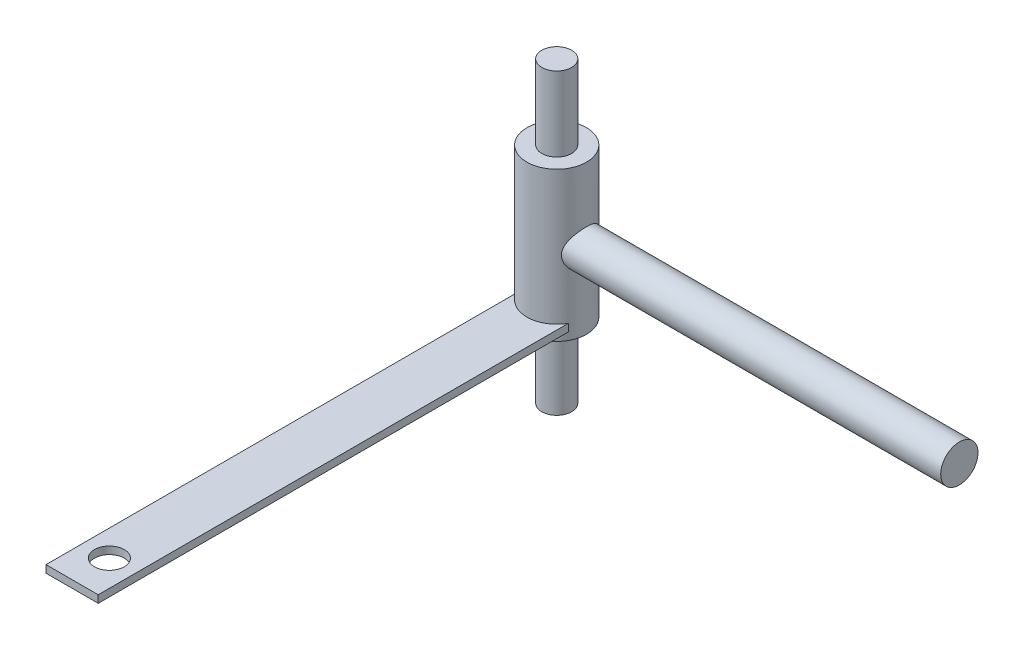
SolidWorks part; units mm, degrees
ref_plane "Front Plane" through (0, 0, 0) normal (0, 0, 1) x (1, 0, 0)
ref_plane "Top Plane" through (0, 0, 0) normal (0, 1, 0) x (1, 0, 0)
ref_plane "Right Plane" through (0, 0, 0) normal (1, 0, 0) x (0, 0, -1)
sketch "Sketch1" plane through (0, 0, 0) normal (0, 1, 0) x (1, 0, 0)
  circle A0 centre (0, 0) radius 4
  dimension "D1" = 8
extrude "Boss-Extrude1" add sketch "Sketch1" along normal mid plane 80
sketch "Sketch3" plane through (0, 0, 0) normal (0, 1, 0) x (1, 0, 0)
  circle A0 centre (0, 0) radius 8
  dimension "D1" = 16
extrude "Boss-Extrude2" add sketch "Sketch3" along normal mid plane 40
sketch "Sketch4" plane through (0, 0, 0) normal (1, 0, 0) x (0, 0, -1)
  circle A0 centre (0, 0) radius 5
  dimension "D1" = 10
extrude "Boss-Extrude3" add sketch "Sketch4" along normal blind 108
sketch "Sketch5" plane through (0, 0, 0) normal (0, 0, 1) x (1, 0, 0)
  line L0 (-8, -20) -> (8, -20) construction
  line L5 (-7, -16) -> (7, -16)
  line L6 (-7, -16) -> (-7, -18)
  line L7 (-7, -18) -> (7, -18)
  line L8 (7, -16) -> (7, -18)
  line L9 (-7, -16) -> (7, -18) construction
  line L10 (-7, -18) -> (7, -16) construction
  point P0 (0, -17)
  point P5 (0.1078, -15.9091)
  point P10 (0, 0)
  dimension "D1" = 14
  dimension "D2" = 2
  dimension "D3" = 2
extrude "Boss-Extrude4" add sketch "Sketch5" along normal blind 130
sketch "Sketch6" plane through (0, -16, 0) normal (0, 1, 0) x (1, 0, 0)
  line L0 (7, -130) -> (-7, -130) construction
  circle A0 centre (0, -120) radius 4
  point P4 (0, -130)
  dimension "D1" = 8
  dimension "D2" = 10
extrude "Cut-Extrude1" cut sketch "Sketch6" against normal up to next
